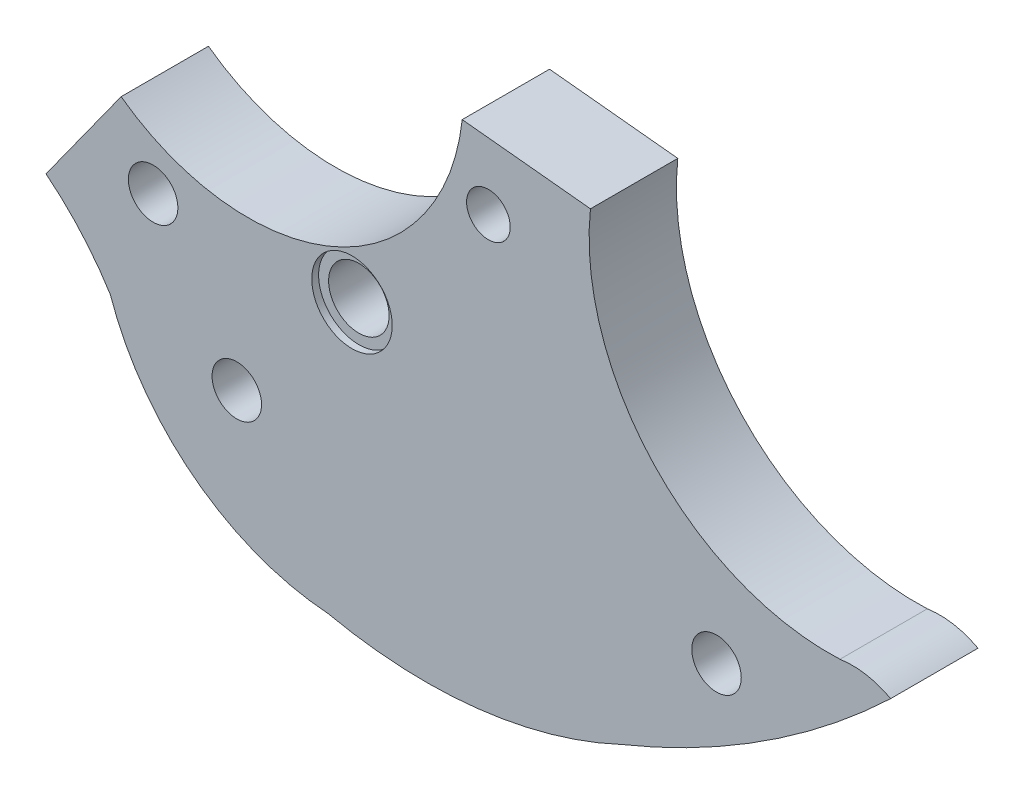
SolidWorks part; units mm, degrees
ref_plane "Plano frontal" through (0, 0, 0) normal (0, 0, 1) x (1, 0, 0)
ref_plane "Plano superior" through (0, 0, 0) normal (0, 1, 0) x (1, 0, 0)
ref_plane "Plano direito" through (0, 0, 0) normal (1, 0, 0) x (0, 0, -1)
sketch "Esboço1" plane through (0, 0, 0) normal (0, 0, 1) x (1, 0, 0)
  line L0 (148.8333, 304.5) -> (744.1667, 304.5) construction
  line L1 (67.9858, 79.9575) -> (86.6256, 78.4584) construction
  line L2 (68.264, 80.4715) -> (86.9137, 78.5649)
  line L3 (67.3704, 80.5628) -> (68.264, 80.4715) construction
  line L4 (86.9137, 78.5649) -> (88.4593, 78.4069) construction
  line L5 (7.741, 43.3814) -> (18.6636, 58.5601)
  arc A0 (86.9137, 78.5649) -> (123.1994, 39.9806) centre (121.6121, 74.842) ccw
  arc A1 (18.6636, 58.5601) -> (68.264, 80.4715) centre (37.1254, 83.864) ccw
  arc A2 (17.0916, 32.8633) -> (48.7853, 8.5061) centre (51.3919, 44.6963) ccw
  arc A3 (48.7853, 8.5061) -> (91.4217, 13.3565) centre (62.9304, 73.9849) ccw
  arc A4 (91.4217, 13.3565) -> (130.5686, 38.7048) centre (44.4653, 128.7765) ccw
  arc A5 (130.5686, 38.7048) -> (123.1994, 39.9806) centre (124.9786, 28.3369) ccw
  arc A6 (17.0916, 32.8633) -> (7.741, 43.3814) centre (-18.3333, 10.7859) ccw
  circle A7 centre (72.0734, 70.4201) radius 3.175
  circle A8 centre (23.3183, 48.679) radius 3.6
  circle A9 centre (35.4865, 29.9885) radius 3.6
  circle A10 centre (105.2437, 30.4641) radius 3.6
  circle A11 centre (52.2343, 49.4577) radius 4.4
  point P4 (86.7759, 76.9104)
  point P5 (97.2984, 49.8084)
  point P6 (123.1994, 39.9806)
  point P7 (47.851, 54.4347)
  point P8 (67.6667, 76.9104)
  point P9 (20.3708, 57.3988)
  point P11 (13.0565, 38.2998)
  point P12 (83.7679, 78.8865)
  point P13 (71.2324, 80.168)
  point P14 (43.9003, 9.1941)
  point P16 (72.0734, 70.4201)
  point P17 (19.6083, 27.194)
  point P22 (79.9514, 9.1941)
  point P23 (32.5173, 13.708)
  point P26 (91.4217, 13.3565)
  point P27 (128.4816, 36.7551)
  point P28 (48.7853, 8.5061)
  point P32 (108.1172, 21.6545)
  point P33 (129.1865, 39.3385)
  point P34 (23.3183, 48.679)
  point P36 (17.0916, 32.8633)
  point P37 (126.7579, 39.9806)
  point P38 (7.741, 43.3814)
  point P39 (15.2948, 53.8786)
  point P43 (52.2343, 49.4577)
  point P47 (35.4865, 29.9885)
  point P49 (105.2437, 30.4641)
extrude "Ressalto-extrusão1" add sketch "Esboço1" along normal blind 12.7
sketch "Esboço3" plane through (0, 0, 12.7) normal (0, 0, 1) x (1, 0, 0)
  circle A0 centre (52.2343, 49.4577) radius 5.85
  circle A1 centre (52.2343, 49.4577) radius 4.4 construction
  dimension "D1" = 11.7
extrude "Corte-extrusão1" cut sketch "Esboço3" against normal blind 1
